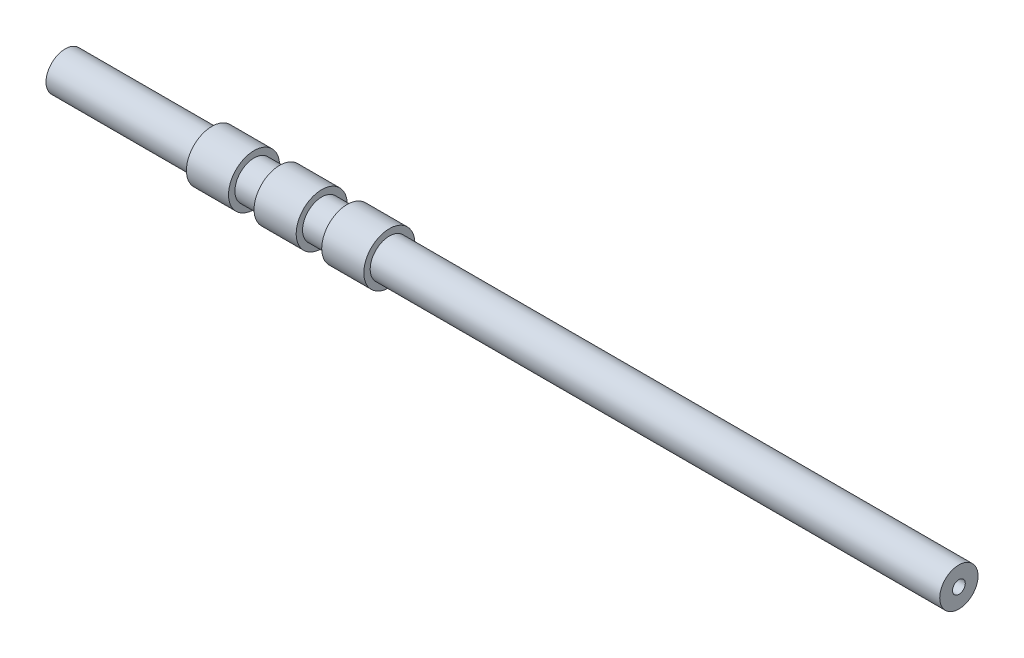
SolidWorks part; units mm, degrees
ref_plane "Front Plane" through (0, 0, 0) normal (0, 0, 1) x (1, 0, 0)
ref_plane "Top Plane" through (0, 0, 0) normal (0, 1, 0) x (1, 0, 0)
ref_plane "Right Plane" through (0, 0, 0) normal (1, 0, 0) x (0, 0, -1)
sketch "Sketch1" plane through (0, 0, 0) normal (0, 0, 1) x (1, 0, 0)
  line L0 (-114.6032, 0) -> (114.6032, 0) construction
  line L1 (-152.6984, 15) -> (-62.6984, 15)
  line L2 (-62.6984, 15) -> (-62.6984, 20)
  line L3 (-62.6984, 20) -> (-29.7284, 20)
  line L4 (-29.7284, 20) -> (-29.7284, 15)
  line L5 (-29.7284, 15) -> (-9.7284, 15)
  line L6 (-9.7284, 15) -> (-9.7284, 20)
  line L7 (-9.7284, 20) -> (23.2416, 20)
  line L8 (23.2416, 20) -> (23.2416, 15)
  line L9 (23.2416, 15) -> (43.2416, 15)
  line L10 (43.2416, 15) -> (43.2416, 20)
  line L11 (43.2416, 20) -> (76.2116, 20)
  line L12 (76.2116, 20) -> (76.2116, 15)
  line L13 (76.2116, 15) -> (192.2378, 15)
  line L14 (192.2378, 15) -> (497.3016, 15)
  line L15 (-152.6984, 15) -> (-177.6984, 15)
  line L16 (497.3016, 15) -> (522.3016, 15)
  point P4 (0, 0)
  dimension "D2" = 15
  dimension "D3" = 15
  dimension "D4" = 32.97
  dimension "D5" = 15
  dimension "D6" = 20
  dimension "D7" = 15
  dimension "D8" = 32.97
  dimension "D9" = 32.97
  dimension "D10" = 20
  dimension "D11" = 20
  dimension "D12" = 20
  dimension "D13" = 20
  dimension "D14" = 650
  dimension "D15" = 90
  dimension "D16" = 25
  dimension "D17" = 25
revolve "Revolve-Thin1" add sketch "Sketch1" angle 360 about L0
